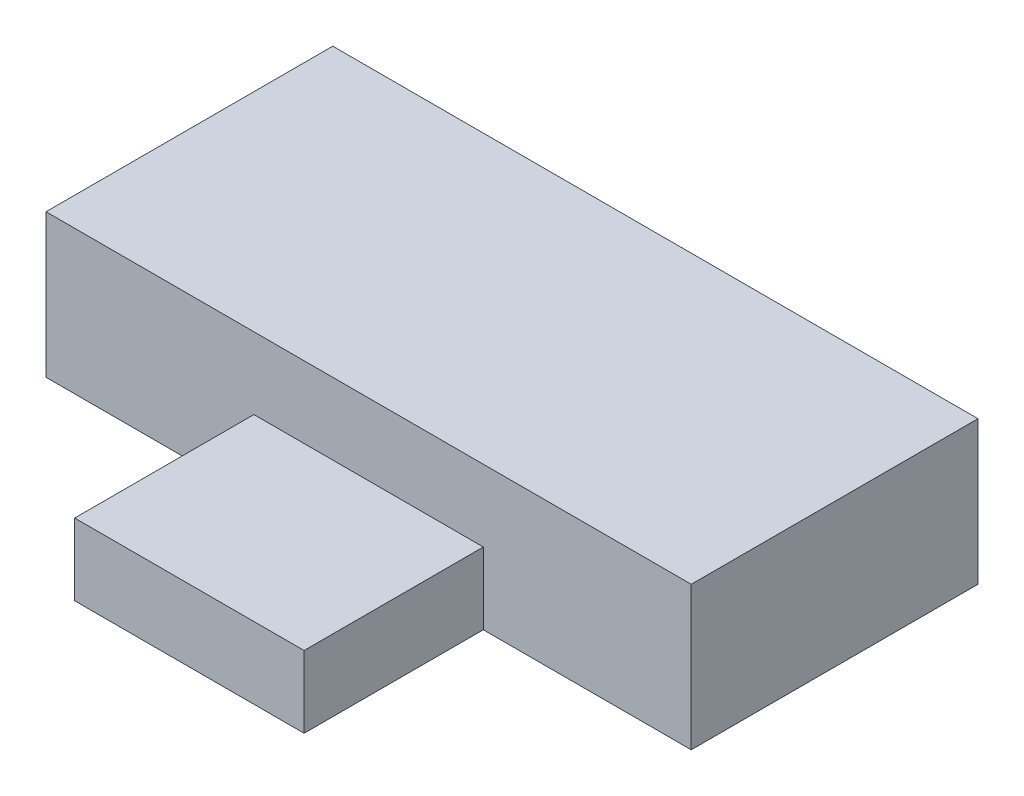
SolidWorks part; units mm, degrees
ref_plane "Plan de face" through (0, 0, 0) normal (0, 0, 1) x (1, 0, 0)
ref_plane "Plan de dessus" through (0, 0, 0) normal (0, 1, 0) x (1, 0, 0)
ref_plane "Plan de droite" through (0, 0, 0) normal (1, 0, 0) x (0, 0, -1)
sketch "Esquisse1" plane through (0, 0, 0) normal (0, 1, 0) x (1, 0, 0)
  line L1 (-9, 4) -> (9, 4)
  line L2 (-9, 4) -> (-9, -4)
  line L3 (-9, -4) -> (9, -4)
  line L4 (9, 4) -> (9, -4)
  line L5 (-9, 4) -> (9, -4) construction
  line L6 (-9, -4) -> (9, 4) construction
  point P0 (0, 0)
  dimension "D1" = 18
  dimension "D2" = 8
extrude "Boss.-Extru.1" add sketch "Esquisse1" along normal blind 4
sketch "Esquisse2" plane through (0, 0, 4) normal (0, 0, 1) x (1, 0, 0)
  line L0 (0, 1) -> (0, 0) construction
  line L1 (-3.2, 2) -> (3.2, 2)
  line L2 (-3.2, 2) -> (-3.2, 0)
  line L3 (-3.2, 0) -> (3.2, 0)
  line L4 (3.2, 2) -> (3.2, 0)
  line L5 (-3.2, 2) -> (3.2, 0) construction
  line L6 (-3.2, 0) -> (3.2, 2) construction
  line L7 (-9, 0) -> (9, 0) construction
  point P0 (0, 1)
  dimension "D1" = 2
  dimension "D2" = 6.4
extrude "Boss.-Extru.2" add sketch "Esquisse2" along normal blind 5
